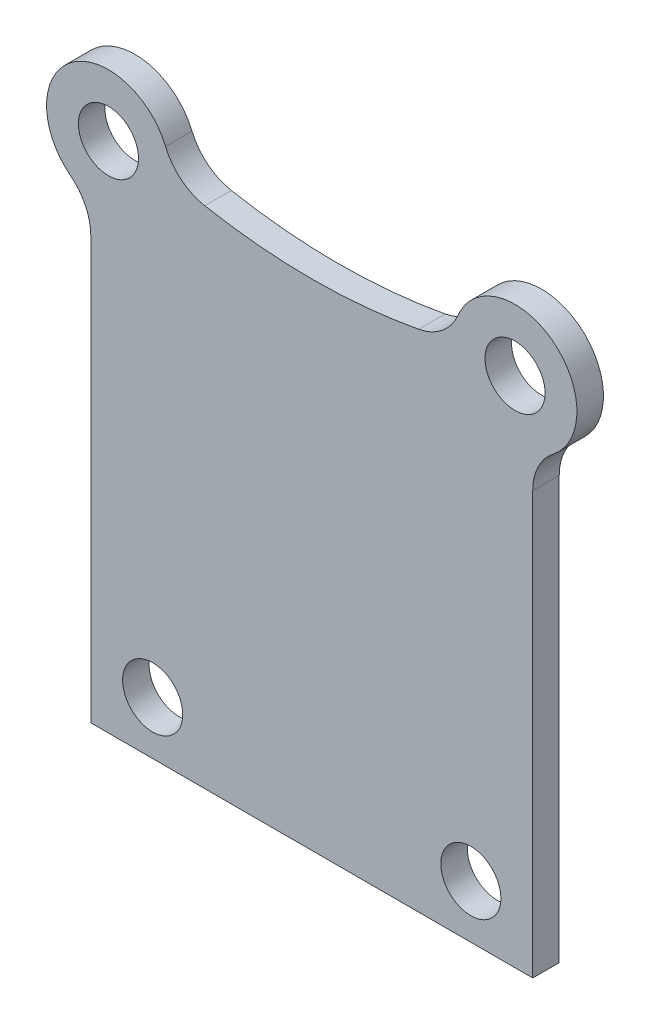
SolidWorks part; units mm, degrees
material "Сплав 2024"
ref_plane "Спереди" through (0, 0, 0) normal (0, 0, 1) x (1, 0, 0)
ref_plane "Сверху" through (0, 0, 0) normal (0, 1, 0) x (1, 0, 0)
ref_plane "Справа" through (0, 0, 0) normal (1, 0, 0) x (0, 0, -1)
sketch "Эскиз1" plane through (0, 0, 0) normal (0, 0, 1) x (1, 0, 0)
  line L0 (-12.5, -56.1235) -> (-12.5, -80) construction
  line L1 (12.5, -80) -> (12.5, -56.1235) construction
  line L2 (-12.5, -56.1235) -> (-12.5, -80)
  line L3 (12.5, -80) -> (12.5, -56.1235)
  line L4 (-12.5, -80) -> (12.5, -80)
  arc A0 (-12.5, -56.1235) -> (-13.6538, -53.7588) centre (-15.5, -56.1235) ccw construction
  arc A1 (-8.2704, -49.6511) -> (-13.6538, -53.7588) centre (-11.5, -51) ccw construction
  arc A2 (-8.2704, -49.6511) -> (-6.0523, -51.444) centre (-5.5021, -48.4949) ccw construction
  arc A3 (-6.0523, -51.444) -> (6.0523, -51.444) centre (0, -19) ccw construction
  arc A4 (6.0523, -51.444) -> (8.2704, -49.6511) centre (5.5021, -48.4949) ccw construction
  arc A5 (13.6538, -53.7588) -> (8.2704, -49.6511) centre (11.5, -51) ccw construction
  arc A6 (13.6538, -53.7588) -> (12.5, -56.1235) centre (15.5, -56.1235) ccw construction
  arc A7 (-12.5, -56.1235) -> (-13.6538, -53.7588) centre (-15.5, -56.1235) ccw
  arc A8 (-8.2704, -49.6511) -> (-13.6538, -53.7588) centre (-11.5, -51) ccw
  arc A9 (-8.2704, -49.6511) -> (-6.0523, -51.444) centre (-5.5021, -48.4949) ccw
  arc A10 (-6.0523, -51.444) -> (6.0523, -51.444) centre (0, -19) ccw
  arc A11 (6.0523, -51.444) -> (8.2704, -49.6511) centre (5.5021, -48.4949) ccw
  arc A12 (13.6538, -53.7588) -> (8.2704, -49.6511) centre (11.5, -51) ccw
  arc A13 (13.6538, -53.7588) -> (12.5, -56.1235) centre (15.5, -56.1235) ccw
extrude "Бобышка-Вытянуть1" add sketch "Эскиз1" against normal blind 1.5
hole_wizard "Отверстие с зазором M31" positions "Эскиз3" profile "Эскиз2" hole size "M3" standard "Ansi Metric" end condition up to next
sketch "Эскиз3" plane through (0, 0, 0) normal (0, 0, 1) x (1, 0, 0)
  point P0 (11.5, -51)
  point P3 (-11.5, -51)
  point P6 (9, -77)
  point P9 (-9, -77)
sketch "Эскиз2" plane through (11.5, -51, 0) normal (1, 0, 0) x (0, -1, 0)
  line L0 (0, 0) -> (0, 1.5)
  line L1 (0, 1.5) -> (1.7, 1.5)
  line L2 (1.7, 1.5) -> (1.7, 0)
  line L5 (1.7, 0) -> (0, 0)
  line L11 (0, -6.35) -> (0, 107.95) construction
  dimension "Диаметр сквозного отверстия" = 3.4
  dimension "Глубина сквозного отверстия" = 1.5
